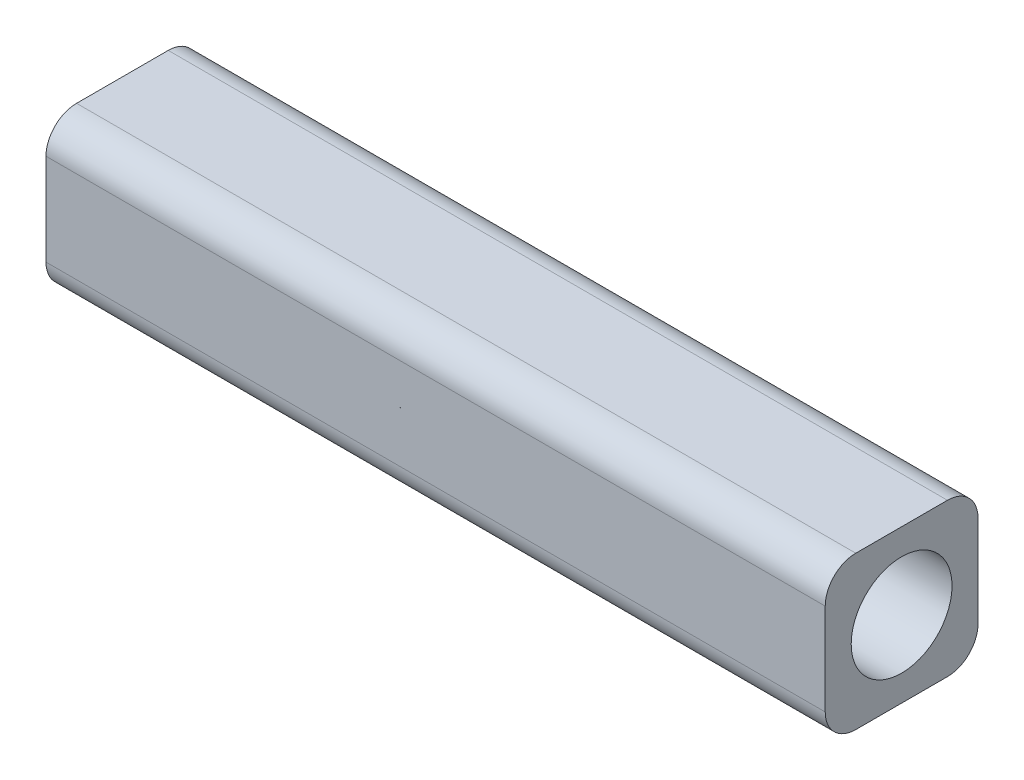
SolidWorks part; units mm, degrees
ref_plane "前视基准面" through (0, 0, 0) normal (0, 0, 1) x (1, 0, 0)
ref_plane "上视基准面" through (0, 0, 0) normal (0, 1, 0) x (1, 0, 0)
ref_plane "右视基准面" through (0, 0, 0) normal (1, 0, 0) x (0, 0, -1)
sketch "Sketch1" plane through (0, 0, 0) normal (0, 1, 0) x (1, 0, 0)
  line L1 (-12.75, -2.5) -> (12.75, -2.5)
  line L2 (-12.75, -2.5) -> (-12.75, 2.5)
  line L3 (-12.75, 2.5) -> (12.75, 2.5)
  line L4 (12.75, -2.5) -> (12.75, 2.5)
  line L5 (-12.75, -2.5) -> (12.75, 2.5) construction
  line L6 (-12.75, 2.5) -> (12.75, -2.5) construction
  point P0 (0, 0)
  dimension "D1" = 25.5
  dimension "D2" = 5
extrude "Boss-Extrude1" add sketch "Sketch1" along normal blind 5
sketch "Sketch2" plane through (12.75, 0, 0) normal (1, 0, 0) x (0, 0, -1)
  line L0 (-2.5, 5) -> (2.5, 0) construction
  circle A0 centre (0, 2.5) radius 1.65
  point P6 (0, 0)
  dimension "D1" = 3.3
extrude "Cut-Extrude1" cut sketch "Sketch2" against normal through all both and the other way through all
fillet "Fillet1" radius 1 4 edges at (0, 0, -2.5) (0, 0, 2.5) (0, 5, -2.5) (0, 5, 2.5)
